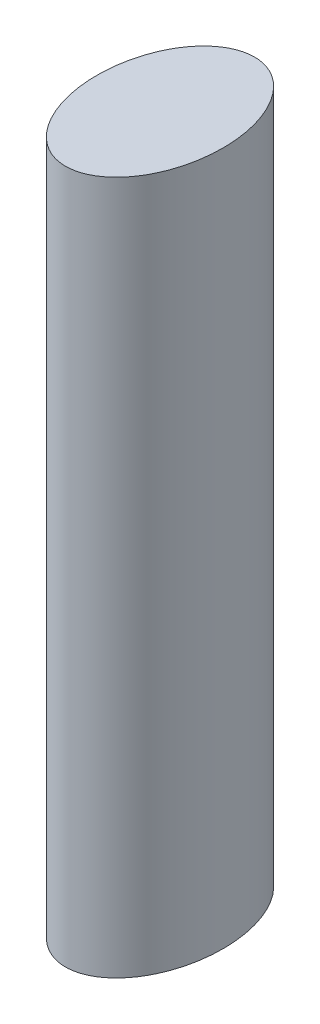
SolidWorks part; units mm, degrees
ref_plane "Front Plane" through (0, 0, 0) normal (0, 0, 1) x (1, 0, 0)
ref_plane "Top Plane" through (0, 0, 0) normal (0, 1, 0) x (1, 0, 0)
ref_plane "Right Plane" through (0, 0, 0) normal (1, 0, 0) x (0, 0, -1)
sketch "Sketch2" plane through (0, 0, 0) normal (0, 1, 0) x (1, 0, 0)
  ellipse E0 centre (0, 0) end of major axis (0, 15) minor radius 10
  dimension "D1" = 30
  dimension "D2" = 20
extrude "Boss-Extrude1" add sketch "Sketch2" along normal blind 110
